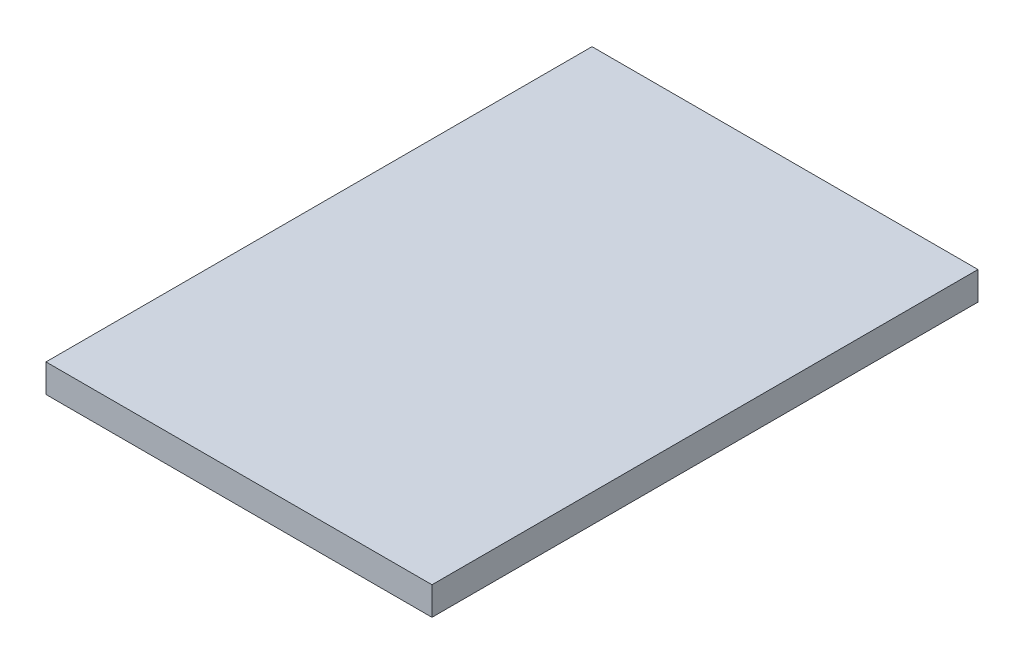
SolidWorks part; units mm, degrees
ref_plane "Plan de face" through (0, 0, 0) normal (0, 0, 1) x (1, 0, 0)
ref_plane "Plan de dessus" through (0, 0, 0) normal (0, 1, 0) x (1, 0, 0)
ref_plane "Plan de droite" through (0, 0, 0) normal (1, 0, 0) x (0, 0, -1)
sketch "Esquisse1" plane through (0, 0, 0) normal (0, 0, 1) x (1, 0, 0)
  line L0 (0, 0) -> (-30, 0)
  line L1 (0, 0) -> (350, 0)
  line L2 (0, 0) -> (0, 30)
  line L3 (0, 30) -> (350, 30)
  line L4 (350, 0) -> (350, 30)
  line L5 (350, 30) -> (380, 30)
  line L6 (350, 30) -> (350, 170)
  line L7 (350, 170) -> (380, 170)
  line L8 (380, 30) -> (380, 170)
  line L9 (0, 30) -> (-30, 30)
  line L10 (0, 30) -> (0, 170)
  line L11 (0, 170) -> (-30, 170)
  line L12 (-30, 30) -> (-30, 170)
  line L13 (-30, 0) -> (-30, 30)
  line L14 (350, 0) -> (380, 0)
  line L15 (380, 0) -> (380, 30)
  line L16 (350, 170) -> (380, 152.6815)
  line L17 (380, 152.6815) -> (380, 170)
  line L18 (380, 170) -> (380, 187.3215)
  line L19 (350, 170) -> (380, 187.3215)
  line L20 (-30, 170) -> (0, 152.6815)
  line L21 (0, 170) -> (0, 187.3215)
  line L22 (0, 187.3215) -> (-30, 170)
  line L23 (0, 170) -> (-30, 152.6815)
  line L24 (-30, 152.6815) -> (-30, 187.3185)
  line L25 (-30, 187.3185) -> (0, 170)
  dimension "D1" = 30
  dimension "D2" = 350
  dimension "D3" = 30
  dimension "D4" = 30
  dimension "D5" = 140
  dimension "D6" = 140
  dimension "D7" = 34.64
  dimension "D8" = 34.64
  dimension "D9" = 34.6415
  dimension "D10" = 34.64
  dimension "D11" = 34.64
  dimension "D12" = 34.64
  dimension "D13" = 34.64
  dimension "D14" = 34.637
extrude "Boss.-Extru.1" add sketch "Esquisse1" along normal blind 580 contours L13 L0 L2 L9 | L1 L4 L3 L2 | L14 L15 L5 L4 | L23 L24 L25 | L11
